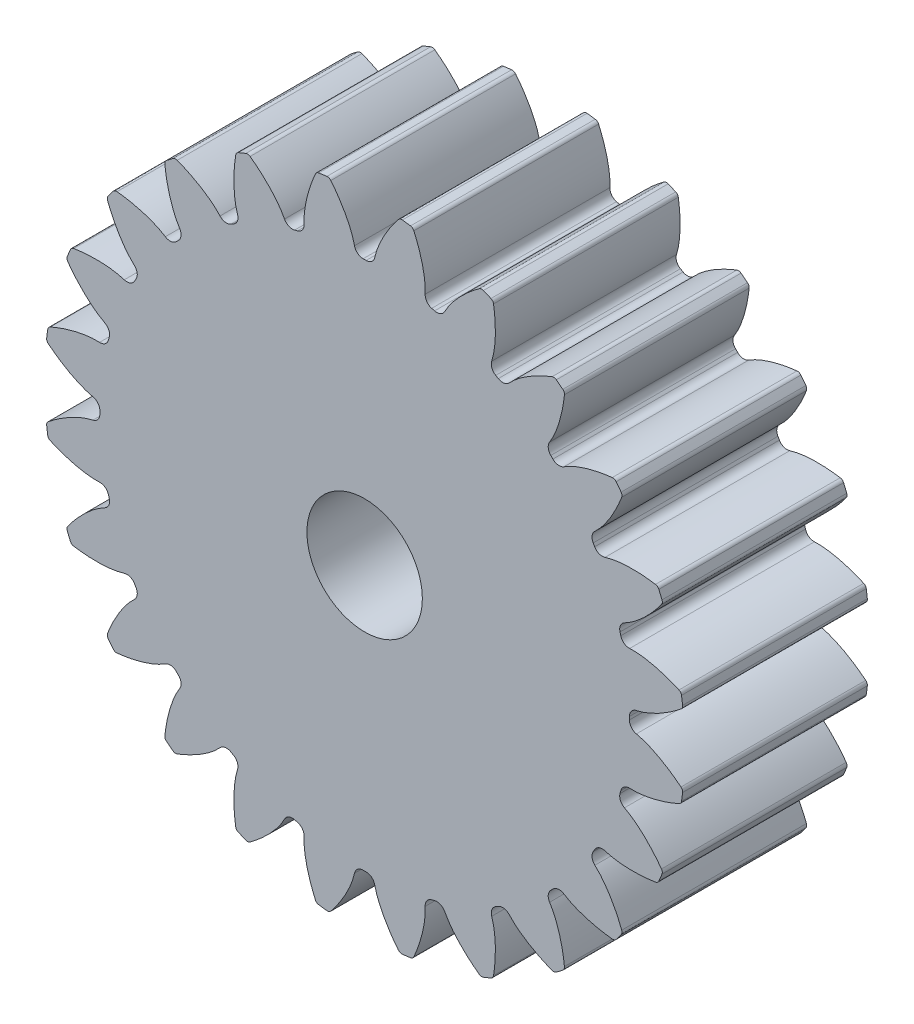
SolidWorks part; units mm, degrees
material "DELRIN"
ref_plane "Front" through (0, 0, 0) normal (0, 0, 1) x (1, 0, 0)
ref_plane "Top" through (0, 0, 0) normal (0, 1, 0) x (1, 0, 0)
ref_plane "Right" through (0, 0, 0) normal (1, 0, 0) x (0, 0, -1)
sketch "Sketch1" plane through (0, 0, 0) normal (0, 0, 1) x (1, 0, 0)
  circle A0 centre (0, 0) radius 22.0133
extrude "Boss-Extrude1" add sketch "Sketch1" along normal blind 12.7
sketch "Sketch3" plane through (0, 0, 0) normal (0, 0, 1) x (1, 0, 0)
  line L0 (0, 0) -> (43.7181, 0) construction
  line L2 (0, 0) -> (-0.6456, 18.1919) construction
  line L3 (0, 0) -> (0.6456, 18.1919) construction
  line L4 (0.6456, 18.1919) -> (0.6532, 18.4046) construction
  line L5 (0, 0) -> (0, 61.276) construction
  line L6 (-0.6456, 18.1919) -> (-0.6532, 18.4046) construction
  circle A0 centre (0, 0) radius 22.0133 construction
  circle A1 centre (0, 0) radius 20.32 construction
  circle A2 centre (0, 0) radius 18.4162 construction
  arc A3 (0.6456, 18.1919) -> (-0.6456, 18.1919) centre (0, 0) ccw construction
  arc A5 (2.4284, 21.879) -> (-2.4284, 21.879) centre (0, 0) ccw
  spline S0 degree 4 poles (-0.6532, 18.4046) (-0.6535, 18.4104) (-0.6545, 18.4268) (-0.6575, 18.4576) (-0.6638, 18.5078) (-0.6738, 18.5716) (-0.6892, 18.6539) (-0.7103, 18.7504) (-0.7366, 18.856) (-0.7687, 18.9703) (-0.8037, 19.0839) (-0.8414, 19.1967) (-0.8815, 19.3085) (-0.9329, 19.4434) (-0.9987, 19.6042) (-1.0815, 19.7907) (-1.1824, 20.0005) (-1.2926, 20.2122) (-1.4071, 20.4189) (-1.5297, 20.6255) (-1.6532, 20.8239) (-1.7884, 21.0275) (-1.9168, 21.2143) (-2.0682, 21.4208) (-2.1926, 21.5866) (-2.3648, 21.8022) (-2.4689, 21.9286) (-2.5935, 22.0754) (-2.6502, 22.14) (-2.6851, 22.1798) knots 0 0 0 0 0 0.005377 0.015084 0.028532 0.04661 0.064855 0.092111 0.119476 0.146842 0.174209 0.201575 0.228941 0.256307 0.307035 0.361767 0.4165 0.471232 0.525964 0.580697 0.635429 0.690161 0.744894 0.799626 0.854358 0.909091 0.954545 1 1 1 1 1 construction
  spline S1 degree 4 poles (-0.6532, 18.4046) (-0.6535, 18.4104) (-0.6545, 18.4268) (-0.6575, 18.4576) (-0.6638, 18.5078) (-0.6738, 18.5716) (-0.6892, 18.6539) (-0.7103, 18.7504) (-0.7366, 18.856) (-0.7687, 18.9703) (-0.8037, 19.0839) (-0.8414, 19.1967) (-0.8815, 19.3085) (-0.9329, 19.4434) (-0.9987, 19.6042) (-1.0815, 19.7907) (-1.1824, 20.0005) (-1.2926, 20.2122) (-1.4071, 20.4189) (-1.5297, 20.6255) (-1.6532, 20.8239) (-1.7884, 21.0275) (-1.9168, 21.2143) (-2.0682, 21.4208) (-2.1926, 21.5866) (-2.3275, 21.7555) (-2.394, 21.8373) (-2.4284, 21.879) knots 0 0 0 0 0 0.005377 0.015084 0.028532 0.04661 0.064855 0.092111 0.119476 0.146842 0.174209 0.201575 0.228941 0.256307 0.307035 0.361767 0.4165 0.471232 0.525964 0.580697 0.635429 0.690161 0.744894 0.799626 0.854358 0.909091 0.909091 0.909091 0.909091 0.909091
  spline S2 degree 4 poles (0.6532, 18.4046) (0.6535, 18.4104) (0.6545, 18.4268) (0.6575, 18.4576) (0.6638, 18.5078) (0.6738, 18.5716) (0.6892, 18.6539) (0.7103, 18.7504) (0.7366, 18.856) (0.7687, 18.9703) (0.8037, 19.0839) (0.8414, 19.1967) (0.8815, 19.3085) (0.9329, 19.4434) (0.9987, 19.6042) (1.0815, 19.7907) (1.1824, 20.0005) (1.2926, 20.2122) (1.4071, 20.4189) (1.5297, 20.6255) (1.6532, 20.8239) (1.7884, 21.0275) (1.9168, 21.2143) (2.0682, 21.4208) (2.1926, 21.5866) (2.3648, 21.8022) (2.4689, 21.9286) (2.5935, 22.0754) (2.6502, 22.14) (2.6851, 22.1798) knots 0 0 0 0 0 0.005377 0.015084 0.028532 0.04661 0.064855 0.092111 0.119476 0.146842 0.174209 0.201575 0.228941 0.256307 0.307035 0.361767 0.4165 0.471232 0.525964 0.580697 0.635429 0.690161 0.744894 0.799626 0.854358 0.909091 0.954545 1 1 1 1 1 construction
  spline S3 degree 4 poles (0.6532, 18.4046) (0.6535, 18.4104) (0.6545, 18.4268) (0.6575, 18.4576) (0.6638, 18.5078) (0.6738, 18.5716) (0.6892, 18.6539) (0.7103, 18.7504) (0.7366, 18.856) (0.7687, 18.9703) (0.8037, 19.0839) (0.8414, 19.1967) (0.8815, 19.3085) (0.9329, 19.4434) (0.9987, 19.6042) (1.0815, 19.7907) (1.1824, 20.0005) (1.2926, 20.2122) (1.4071, 20.4189) (1.5297, 20.6255) (1.6532, 20.8239) (1.7884, 21.0275) (1.9168, 21.2143) (2.0682, 21.4208) (2.1926, 21.5866) (2.3275, 21.7555) (2.394, 21.8373) (2.4284, 21.879) knots 0 0 0 0 0 0.005377 0.015084 0.028532 0.04661 0.064855 0.092111 0.119476 0.146842 0.174209 0.201575 0.228941 0.256307 0.307035 0.361767 0.4165 0.471232 0.525964 0.580697 0.635429 0.690161 0.744894 0.799626 0.854358 0.909091 0.909091 0.909091 0.909091 0.909091
  point P0 (0, 18.2033)
sketch "DCLTBC" plane through (0, 0, 0) normal (0, 0, 1) x (1, 0, 0)
  line L0 (0, 0) -> (41.04, 0) construction
  line L1 (-0.6456, 18.1919) -> (-0.6532, 18.4046) construction
  line L2 (0.6456, 18.1919) -> (0.6532, 18.4046) construction
  line L3 (-0.6456, 18.1919) -> (-0.6532, 18.4046)
  line L4 (0.6456, 18.1919) -> (0.6532, 18.4046)
  line L5 (0, 0) -> (0, 104.9356) construction
  circle A0 centre (0, 0) radius 22.0133
  circle A1 centre (0, 0) radius 20.32 construction
  circle A2 centre (0, 0) radius 18.4162 construction
  arc A3 (0.6456, 18.1919) -> (-0.6456, 18.1919) centre (0, 0) ccw construction
  arc A4 (0.6456, 18.1919) -> (-0.6456, 18.1919) centre (0, 0) ccw
  spline S0 degree 4 poles (-999.1981, -34.6963) (-14.3386, 16.1827) (-0.8334, 17.2583) (-0.5869, 17.8923) (-0.6638, 18.5078) (-0.6738, 18.5716) (-0.6892, 18.6539) (-0.7103, 18.7504) (-0.7366, 18.856) (-0.7687, 18.9703) (-0.8037, 19.0839) (-0.8414, 19.1967) (-0.8815, 19.3085) (-0.9329, 19.4434) (-0.9987, 19.6042) (-1.0815, 19.7907) (-1.1824, 20.0005) (-1.2926, 20.2122) (-1.4071, 20.4189) (-1.5297, 20.6255) (-1.6532, 20.8239) (-1.7884, 21.0275) (-1.9168, 21.2143) (-2.0682, 21.4208) (-2.6456, 22.1903) (-4.6145, 24.4426) (15.9918, -0.7638) (-639.5408, 792.6401) knots -0.524597 -0.524597 -0.524597 -0.524597 -0.524597 0.005377 0.015084 0.028532 0.04661 0.064855 0.092111 0.119476 0.146842 0.174209 0.201575 0.228941 0.256307 0.307035 0.361767 0.4165 0.471232 0.525964 0.580697 0.635429 0.690161 0.744894 0.799626 0.854358 1.706051 1.706051 1.706051 1.706051 1.706051 only from (-0.6532, 18.4046) to (-2.4284, 21.879) construction
  spline S1 degree 4 poles (999.1981, -34.6963) (14.3386, 16.1827) (0.8334, 17.2583) (0.5869, 17.8923) (0.6638, 18.5078) (0.6738, 18.5716) (0.6892, 18.6539) (0.7103, 18.7504) (0.7366, 18.856) (0.7687, 18.9703) (0.8037, 19.0839) (0.8414, 19.1967) (0.8815, 19.3085) (0.9329, 19.4434) (0.9987, 19.6042) (1.0815, 19.7907) (1.1824, 20.0005) (1.2926, 20.2122) (1.4071, 20.4189) (1.5297, 20.6255) (1.6532, 20.8239) (1.7884, 21.0275) (1.9168, 21.2143) (2.0682, 21.4208) (2.6456, 22.1903) (4.6145, 24.4426) (-15.9918, -0.7638) (639.5408, 792.6401) knots -0.524597 -0.524597 -0.524597 -0.524597 -0.524597 0.005377 0.015084 0.028532 0.04661 0.064855 0.092111 0.119476 0.146842 0.174209 0.201575 0.228941 0.256307 0.307035 0.361767 0.4165 0.471232 0.525964 0.580697 0.635429 0.690161 0.744894 0.799626 0.854358 1.706051 1.706051 1.706051 1.706051 1.706051 only from (0.6532, 18.4046) to (2.4284, 21.879) construction
  spline S2 degree 4 poles (-0.6532, 18.4046) (-0.6535, 18.4104) (-0.6545, 18.4268) (-0.6575, 18.4576) (-0.6638, 18.5078) (-0.6738, 18.5716) (-0.6892, 18.6539) (-0.7103, 18.7504) (-0.7366, 18.856) (-0.7687, 18.9703) (-0.8037, 19.0839) (-0.8414, 19.1967) (-0.8815, 19.3085) (-0.9329, 19.4434) (-0.9987, 19.6042) (-1.0815, 19.7907) (-1.1824, 20.0005) (-1.2926, 20.2122) (-1.4071, 20.4189) (-1.5297, 20.6255) (-1.6532, 20.8239) (-1.7884, 21.0275) (-1.9168, 21.2143) (-2.0682, 21.4208) (-2.1926, 21.5866) (-2.3275, 21.7555) (-2.394, 21.8373) (-2.4284, 21.879) knots 0 0 0 0 0 0.005377 0.015084 0.028532 0.04661 0.064855 0.092111 0.119476 0.146842 0.174209 0.201575 0.228941 0.256307 0.307035 0.361767 0.4165 0.471232 0.525964 0.580697 0.635429 0.690161 0.744894 0.799626 0.854358 0.909091 0.909091 0.909091 0.909091 0.909091
  spline S3 degree 4 poles (0.6532, 18.4046) (0.6535, 18.4104) (0.6545, 18.4268) (0.6575, 18.4576) (0.6638, 18.5078) (0.6738, 18.5716) (0.6892, 18.6539) (0.7103, 18.7504) (0.7366, 18.856) (0.7687, 18.9703) (0.8037, 19.0839) (0.8414, 19.1967) (0.8815, 19.3085) (0.9329, 19.4434) (0.9987, 19.6042) (1.0815, 19.7907) (1.1824, 20.0005) (1.2926, 20.2122) (1.4071, 20.4189) (1.5297, 20.6255) (1.6532, 20.8239) (1.7884, 21.0275) (1.9168, 21.2143) (2.0682, 21.4208) (2.1926, 21.5866) (2.3275, 21.7555) (2.394, 21.8373) (2.4284, 21.879) knots 0 0 0 0 0 0.005377 0.015084 0.028532 0.04661 0.064855 0.092111 0.119476 0.146842 0.174209 0.201575 0.228941 0.256307 0.307035 0.361767 0.4165 0.471232 0.525964 0.580697 0.635429 0.690161 0.744894 0.799626 0.854358 0.909091 0.909091 0.909091 0.909091 0.909091
extrude "Cut-Extrude-DCLTBC" cut sketch "DCLTBC" along normal through all
fillet "Fillet-Tip-DCLTBC" radius 0.3011 2 edges at (2.4284, 21.879, 6.35) (-2.4284, 21.879, 6.35)
fillet "Fillet-Root-DCLTBC" radius 0.6022 2 edges at (-0.6456, 18.1919, 6.35) (0.6456, 18.1919, 6.35)
pattern_circular "CirPattern-DCLTBC" count 24 over 360 about axis through (0, 0, 12.7) along (0, 0, 1) of "Cut-Extrude-DCLTBC", "Fillet-Tip-DCLTBC", "Fillet-Root-DCLTBC"
sketch "DCGTBC" [suppressed] plane through (0, 0, 0) normal (0, 0, 1) x (1, 0, 0)
  line L0 (0, 0) -> (41.04, 0) construction
  line L1 (-60.6226, 5.3038) -> (0, 0) construction
  line L2 (0, 0) -> (60.6226, 5.3038) construction
  line L3 (0, 0) -> (-16.5124, 0)
  line L5 (0, 0) -> (0, 104.9356) construction
  circle A0 centre (0, 0) radius 65.6167
  circle A1 centre (0, 0) radius 63.5 construction
  circle A2 centre (0, 0) radius 57.5505 construction
  arc A3 (-0.231, 60.8537) -> (0.231, 60.8537) centre (0, 0) ccw construction
  arc A11 (60.6226, 5.3038) -> (-60.6226, 5.3038) centre (0, 0) ccw
  spline S4 degree 4 poles (999.5281, 37.5164) (15.9379, 54.4029) (0.0707, 55.4419) (-0.2895, 56.6024) (-0.2066, 57.7767) (-0.1929, 57.9173) (-0.1708, 58.0988) (-0.1393, 58.3123) (-0.0988, 58.5468) (-0.0484, 58.8015) (0.0074, 59.0552) (0.0683, 59.3079) (0.1336, 59.5593) (0.2182, 59.8633) (0.3273, 60.227) (0.4659, 60.6511) (0.6363, 61.1305) (0.824, 61.6174) (1.0202, 62.0951) (1.2316, 62.5758) (1.4455, 63.0396) (1.6812, 63.5192) (1.9056, 63.9609) (2.1719, 64.4533) (3.0421, 66.0274) (5.6872, 70.2084) (-15.0429, 35.5301) (520.7458, 920.9699) knots -0.449335 -0.449335 -0.449335 -0.449335 -0.449335 0.005377 0.015084 0.028532 0.04661 0.064855 0.092111 0.119476 0.146842 0.174209 0.201575 0.228941 0.256307 0.307035 0.361767 0.4165 0.471232 0.525964 0.580697 0.635429 0.690161 0.744894 0.799626 0.854358 1.559054 1.559054 1.559054 1.559054 1.559054 only from (-0.2184, 57.5501) to (2.8092, 65.5565) construction
  spline S5 degree 4 poles (-999.5281, 37.5164) (-15.9379, 54.4029) (-0.0707, 55.4419) (0.2895, 56.6024) (0.2066, 57.7767) (0.1929, 57.9173) (0.1708, 58.0988) (0.1393, 58.3123) (0.0988, 58.5468) (0.0484, 58.8015) (-0.0074, 59.0552) (-0.0683, 59.3079) (-0.1336, 59.5593) (-0.2182, 59.8633) (-0.3273, 60.227) (-0.4659, 60.6511) (-0.6363, 61.1305) (-0.824, 61.6174) (-1.0202, 62.0951) (-1.2316, 62.5758) (-1.4455, 63.0396) (-1.6812, 63.5192) (-1.9056, 63.9609) (-2.1719, 64.4533) (-3.0421, 66.0274) (-5.6872, 70.2084) (15.0429, 35.5301) (-520.7458, 920.9699) knots -0.449335 -0.449335 -0.449335 -0.449335 -0.449335 0.005377 0.015084 0.028532 0.04661 0.064855 0.092111 0.119476 0.146842 0.174209 0.201575 0.228941 0.256307 0.307035 0.361767 0.4165 0.471232 0.525964 0.580697 0.635429 0.690161 0.744894 0.799626 0.854358 1.559054 1.559054 1.559054 1.559054 1.559054 only from (0.2184, 57.5501) to (-2.8092, 65.5565) construction
  spline S6 degree 4 poles (-0.2184, 57.5501) (-0.2183, 57.5629) (-0.2176, 57.5987) (-0.2144, 57.6663) (-0.2066, 57.7767) (-0.1929, 57.9173) (-0.1708, 58.0988) (-0.1393, 58.3123) (-0.0988, 58.5468) (-0.0484, 58.8015) (0.0074, 59.0552) (0.0683, 59.3079) (0.1336, 59.5593) (0.2182, 59.8633) (0.3273, 60.227) (0.4659, 60.6511) (0.6363, 61.1305) (0.824, 61.6174) (1.0202, 62.0951) (1.2316, 62.5758) (1.4455, 63.0396) (1.6812, 63.5192) (1.9056, 63.9609) (2.1719, 64.4533) (2.3911, 64.8499) (2.63, 65.2574) (2.7481, 65.4554) (2.8092, 65.5565) knots 0 0 0 0 0 0.005377 0.015084 0.028532 0.04661 0.064855 0.092111 0.119476 0.146842 0.174209 0.201575 0.228941 0.256307 0.307035 0.361767 0.4165 0.471232 0.525964 0.580697 0.635429 0.690161 0.744894 0.799626 0.854358 0.909091 0.909091 0.909091 0.909091 0.909091
  spline S7 degree 4 poles (0.2184, 57.5501) (0.2183, 57.5629) (0.2176, 57.5987) (0.2144, 57.6663) (0.2066, 57.7767) (0.1929, 57.9173) (0.1708, 58.0988) (0.1393, 58.3123) (0.0988, 58.5468) (0.0484, 58.8015) (-0.0074, 59.0552) (-0.0683, 59.3079) (-0.1336, 59.5593) (-0.2182, 59.8633) (-0.3273, 60.227) (-0.4659, 60.6511) (-0.6363, 61.1305) (-0.824, 61.6174) (-1.0202, 62.0951) (-1.2316, 62.5758) (-1.4455, 63.0396) (-1.6812, 63.5192) (-1.9056, 63.9609) (-2.1719, 64.4533) (-2.3911, 64.8499) (-2.63, 65.2574) (-2.7481, 65.4554) (-2.8092, 65.5565) knots 0 0 0 0 0 0.005377 0.015084 0.028532 0.04661 0.064855 0.092111 0.119476 0.146842 0.174209 0.201575 0.228941 0.256307 0.307035 0.361767 0.4165 0.471232 0.525964 0.580697 0.635429 0.690161 0.744894 0.799626 0.854358 0.909091 0.909091 0.909091 0.909091 0.909091
  dimension "D1" = 5
  dimension "D2" = 5
extrude "Cut-Extrude-DCGTBC" [suppressed] cut sketch "DCGTBC" along normal through all
fillet "Fillet-Tip-DCGTBC" [suppressed] radius 0.3011
pattern_circular "CirPattern-DCGTBC" [suppressed] count 24 over 360
sketch "Sketch8" plane through (0, 0, 0) normal (0, 0, 1) x (1, 0, 0)
  line L0 (18.125, -4.6) -> (21.725, -4.6)
  circle A2 centre (19.925, -7) radius 3
  circle A3 centre (0, 0) radius 3.9688
  dimension "D1" = 6
  dimension "D2" = 7.9375
  dimension "D3" = 3.6
extrude "Cut-Extrude5" cut sketch "Sketch8" along normal blind 25.4
equation "\"DiametralPitch\"= 15'Diametral Pitch"
equation "\"NumTeeth\"= 24'Number of Teeth"
equation "\"PressureAngle\"= 25deg'Pressure Angle"
equation "\"Addendum\"= 1 / \"DiametralPitch\"'Addendum"
equation "\"Dedendum\"= 1.25 / \"DiametralPitch\"'Dedendum"
equation "\"WorkingDepth\"= 2 / \"DiametralPitch\"'Working Depth - here for REF (Not used in building model)"
equation "\"WholeDepth\"= 2.25 / \"DiametralPitch\"'Whole Depth - here for REF (Not used in building model)"
equation "\"Clearance\"= .25 / \"DiametralPitch\"'Clearance"
equation "\"CircularPitch\"= pi / \"DiametralPitch\"'Circular Pitch - here for REF (Not used in building model)"
equation "\"PitchCircle\"= \"NumTeeth\" / \"DiametralPitch\"'Pitch Circle - or - Pitch Diameter"
equation "\"OutsideDiameter\"= ( \"NumTeeth\" + 2 ) / \"DiametralPitch\"'Outside Diameter"
equation "\"Fillet_Root\"= \"Clearance\" * cos ( \"PressureAngle\" ) * tan ( ( 90 + \"PressureAngle\" ) / 2 ) 'Fillet Root"
equation "\"AddendumCircle\"= \"PitchCircle\" + ( 2 * \"Addendum\" )'Addendum Circle - or - Addendum Diameter"
equation "\"DedendumCircle\"= \"PitchCircle\" - ( 2 * \"Dedendum\" )'Dedendum Circle - or - Dedendum Diameter"
equation "\"BaseCircle\"= \"PitchCircle\" * cos ( \"PressureAngle\" )'Base Circle - Base Diameter"
equation "\"PitchAngle\"= 360deg / \"NumTeeth\"'Pitch Angle"
equation "\"Alpha\"= sqr ( \"PitchCircle\" ^ 2 - \"BaseCircle\" ^ 2 ) / \"BaseCircle\" * 180 / PI - \"PressureAngle\"'Alpha - Used for Calculating Beta"
equation "\"Beta\"= ( \"PitchAngle\" / 4 - ( \"Alpha\" - 90 ) )'Beta - Used in definition of the parameters for the parametric equation driven curve"
equation "\"Gamma\"= ( \"PitchAngle\" / 4 - ( \"Alpha\" + 90 ) )'Gamma - Used in definition of the parameters for the parametric equation driven curve"
equation "\"Phi\"= sqr ( ( \"AddendumCircle\" / 2 ) ^ 2 - ( \"BaseCircle\" / 2 ) ^ 2 ) / ( \"BaseCircle\" / 2 )'Phi - Used in definition of the parameters for the parametric equation driven curve"
equation "\"DCGTBC\"= iif ( \"DedendumCircle\" > \"BaseCircle\" , \"unsuppressed\" , \"suppressed\" )'if Dedendum Circle IS GREATER THAN BaseCircle THEN UnsuppressORSuppress FEATURE"
equation "\"DCLTBC\"= iif ( \"DedendumCircle\" - .002 > \"BaseCircle\" , \"suppressed\" , \"unsuppressed\" )'if Dedendum Circle - .002 IS GREATER THAN BaseCircle THEN SuppressORUnsuppress FEATURE"
equation "\"Cut-Extrude-DCGTBC\"= iif ( \"DedendumCircle\" > \"BaseCircle\" , \"unsuppressed\" , \"suppressed\" )'if Dedendum Circle IS GREATER THAN BaseCircle THEN UnsuppressORSuppress FEATURE"
equation "\"Cut-Extrude-DCLTBC\"= iif ( \"DedendumCircle\" - .002 > \"BaseCircle\" , \"suppressed\" , \"unsuppressed\" )'if Dedendum Circle - .002 IS GREATER THAN BaseCircle THEN SuppressORUnsuppress FEATURE"
equation "\"CirPattern-DCGTBC\"= iif ( \"DedendumCircle\" > \"BaseCircle\" , \"unsuppressed\" , \"suppressed\" )'if Dedendum Circle IS GREATER THAN BaseCircle THEN UnsuppressORSuppress FEATURE"
equation "\"CirPattern-DCLTBC\"= iif ( \"DedendumCircle\" - .002 > \"BaseCircle\" , \"suppressed\" , \"unsuppressed\" )'if Dedendum Circle - .002 IS GREATER THAN BaseCircle THEN SuppressORUnsuppress FEATURE"
equation "\"Fillet-Tip-DCGTBC\"= iif ( \"DedendumCircle\" > \"BaseCircle\" , \"unsuppressed\" , \"suppressed\" )'if Dedendum Circle IS GREATER THAN BaseCircle THEN UnsuppressORSuppress FEATURE"
equation "\"Fillet-Tip-DCLTBC\"= iif ( \"DedendumCircle\" - .002 > \"BaseCircle\" , \"suppressed\" , \"unsuppressed\" )'if Dedendum Circle - .002 IS GREATER THAN BaseCircle THEN SuppressORUnsuppress FEATURE"
equation "\"Fillet-Root-DCLTBC\"= iif ( \"DedendumCircle\" - .002 > \"BaseCircle\" , \"suppressed\" , \"unsuppressed\" )'if Dedendum Circle - .002 IS GREATER THAN BaseCircle THEN SuppressORUnsuppress FEATURE"
equation "\"D1@CirPattern-DCGTBC\"= \"NumTeeth\"'Number of Teeth"
equation "\"D1@CirPattern-DCLTBC\"= \"NumTeeth\"'Number of Teeth"
equation "\"D1@Fillet-Tip-DCGTBC\"= \"Fillet_Root\" / 2 'Tip Rad For Large No of Teeth"
equation "\"D1@Fillet-Tip-DCLTBC\"=\"Fillet_Root\" / 2'Tip Rad For Small No of Teeth"
equation "\"D1@Fillet-Root-DCLTBC\"= \"Fillet_Root\"'Fillet Root"
